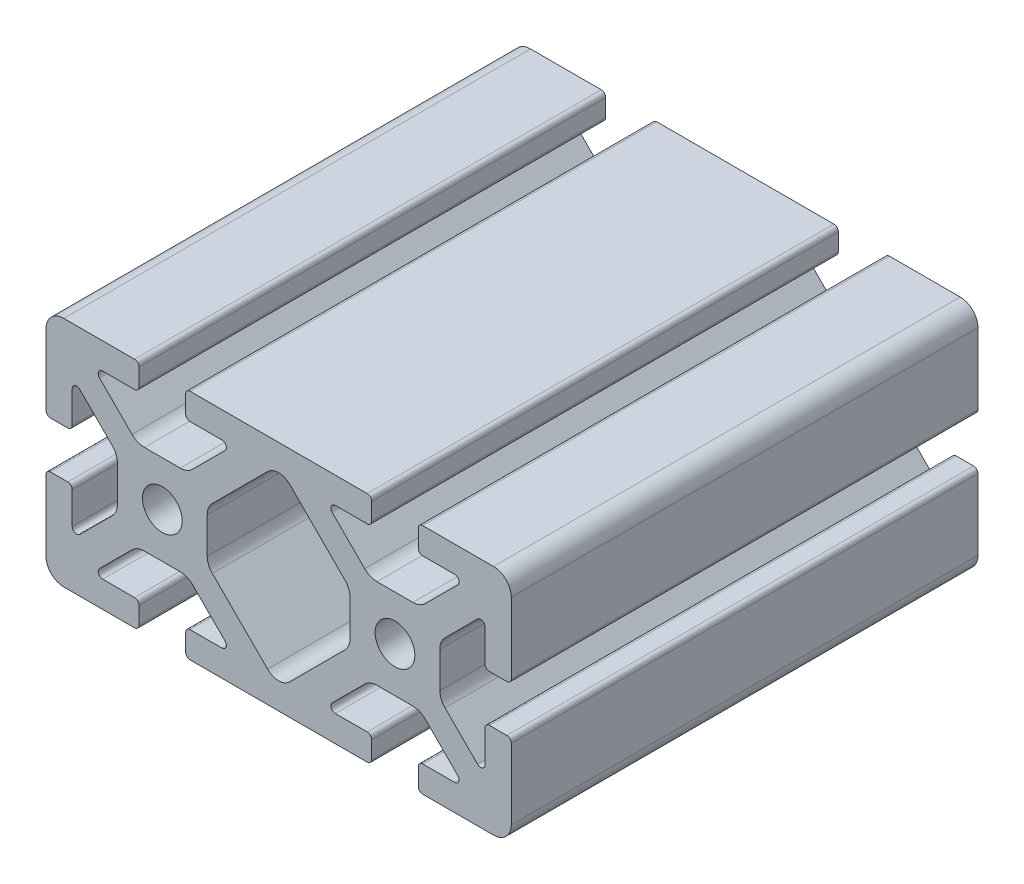
SolidWorks part; units mm, degrees
ref_plane "Front Plane" through (0, 0, 0) normal (0, 0, 1) x (1, 0, 0)
ref_plane "Top Plane" through (0, 0, 0) normal (0, 1, 0) x (1, 0, 0)
ref_plane "Right Plane" through (0, 0, 0) normal (1, 0, 0) x (0, 0, -1)
sketch "Sketch1" plane through (0, 0, 0) normal (0, 0, 1) x (1, 0, 0)
  line L2 (-39.878, 16.891) -> (-39.878, 4.7625)
  line L3 (-36.83, 19.939) -> (-24.7015, 19.939)
  line L4 (-23.9395, 19.177) -> (-23.9395, 16.2052)
  line L5 (-24.7015, 15.4432) -> (-30.1625, 15.4432)
  line L6 (-30.7013, 14.1424) -> (-25.133, 8.5741)
  line L7 (-34.0814, 10.7623) -> (-28.5131, 5.194)
  line L8 (-35.3822, 10.2235) -> (-35.3822, 4.7625)
  line L9 (-36.1442, 4.0005) -> (-39.116, 4.0005)
  line L11 (-23.0136, 7.6962) -> (-16.8644, 7.6962)
  line L12 (-27.6352, 3.0746) -> (-27.6352, -3.0746)
  line L13 (15.1765, 19.939) -> (-15.1765, 19.939)
  line L14 (-15.9385, 19.177) -> (-15.9385, 16.2052)
  line L15 (-15.1765, 15.4432) -> (-9.7155, 15.4432)
  line L16 (-12.2428, 3.0746) -> (-12.2428, -3.0746)
  line L17 (-9.1767, 14.1424) -> (-14.745, 8.5741)
  line L18 (-1.9047, 14.6543) -> (-11.3649, 5.194)
  line L19 (-36.1442, -4.0005) -> (-39.116, -4.0005)
  line L20 (-35.3822, -10.2235) -> (-35.3822, -4.7625)
  line L21 (-34.0814, -10.7623) -> (-28.5131, -5.194)
  line L22 (-30.7013, -14.1424) -> (-25.133, -8.5741)
  line L23 (-24.7015, -15.4432) -> (-30.1625, -15.4432)
  line L24 (-23.9395, -19.177) -> (-23.9395, -16.2052)
  line L25 (-36.83, -19.939) -> (-24.7015, -19.939)
  line L26 (-39.878, -16.891) -> (-39.878, -4.7625)
  line L27 (15.1765, -19.939) -> (-15.1765, -19.939)
  line L28 (-15.9385, -19.177) -> (-15.9385, -16.2052)
  line L29 (-15.1765, -15.4432) -> (-9.7155, -15.4432)
  line L30 (-9.1767, -14.1424) -> (-14.745, -8.5741)
  line L31 (-1.9047, -14.6543) -> (-11.3649, -5.194)
  line L32 (-23.0136, -7.6962) -> (-16.8644, -7.6962)
  line L34 (23.0136, -7.6962) -> (16.8644, -7.6962)
  line L35 (1.9047, -14.6543) -> (11.3649, -5.194)
  line L36 (9.1767, -14.1424) -> (14.745, -8.5741)
  line L37 (15.1765, -15.4432) -> (9.7155, -15.4432)
  line L38 (15.9385, -19.177) -> (15.9385, -16.2052)
  line L40 (39.878, -16.891) -> (39.878, -4.7625)
  line L41 (36.83, -19.939) -> (24.7015, -19.939)
  line L42 (23.9395, -19.177) -> (23.9395, -16.2052)
  line L43 (24.7015, -15.4432) -> (30.1625, -15.4432)
  line L44 (30.7013, -14.1424) -> (25.133, -8.5741)
  line L45 (34.0814, -10.7623) -> (28.5131, -5.194)
  line L46 (35.3822, -10.2235) -> (35.3822, -4.7625)
  line L47 (36.1442, -4.0005) -> (39.116, -4.0005)
  line L48 (1.9047, 14.6543) -> (11.3649, 5.194)
  line L49 (9.1767, 14.1424) -> (14.745, 8.5741)
  line L50 (12.2428, 3.0746) -> (12.2428, -3.0746)
  line L51 (15.1765, 15.4432) -> (9.7155, 15.4432)
  line L52 (15.9385, 19.177) -> (15.9385, 16.2052)
  line L53 (27.6352, 3.0746) -> (27.6352, -3.0746)
  line L54 (23.0136, 7.6962) -> (16.8644, 7.6962)
  line L55 (36.1442, 4.0005) -> (39.116, 4.0005)
  line L56 (35.3822, 10.2235) -> (35.3822, 4.7625)
  line L57 (34.0814, 10.7623) -> (28.5131, 5.194)
  line L58 (30.7013, 14.1424) -> (25.133, 8.5741)
  line L59 (24.7015, 15.4432) -> (30.1625, 15.4432)
  line L60 (23.9395, 19.177) -> (23.9395, 16.2052)
  line L61 (36.83, 19.939) -> (24.7015, 19.939)
  line L62 (39.878, 16.891) -> (39.878, 4.7625)
  circle A0 centre (-19.939, 0) radius 3.4036
  arc A1 (-39.878, 16.891) -> (-36.83, 19.939) centre (-36.83, 16.891) cw
  arc A2 (-34.0814, 10.7623) -> (-35.3822, 10.2235) centre (-34.6202, 10.2235) ccw
  arc A3 (-30.1625, 15.4432) -> (-30.7013, 14.1424) centre (-30.1625, 14.6812) ccw
  arc A4 (-24.7015, 19.939) -> (-23.9395, 19.177) centre (-24.7015, 19.177) cw
  arc A5 (-39.878, 4.7625) -> (-39.116, 4.0005) centre (-39.116, 4.7625) ccw
  arc A6 (-35.3822, 4.7625) -> (-36.1442, 4.0005) centre (-36.1442, 4.7625) cw
  arc A7 (-23.9395, 16.2052) -> (-24.7015, 15.4432) centre (-24.7015, 16.2052) cw
  arc A8 (-23.0136, 7.6962) -> (-25.133, 8.5741) centre (-23.0136, 10.6934) cw
  arc A9 (-27.6352, 3.0746) -> (-28.5131, 5.194) centre (-30.6324, 3.0746) ccw
  arc A10 (1.9047, 14.6543) -> (-1.9047, 14.6543) centre (0, 12.7496) ccw
  arc A11 (-1.9047, -14.6543) -> (1.9047, -14.6543) centre (0, -12.7496) ccw
  arc A12 (-15.1765, 19.939) -> (-15.9385, 19.177) centre (-15.1765, 19.177) ccw
  arc A13 (-15.9385, 16.2052) -> (-15.1765, 15.4432) centre (-15.1765, 16.2052) ccw
  arc A14 (-16.8644, 7.6962) -> (-14.745, 8.5741) centre (-16.8644, 10.6934) ccw
  arc A15 (-12.2428, 3.0746) -> (-11.3649, 5.194) centre (-9.2456, 3.0746) cw
  arc A16 (-9.7155, 15.4432) -> (-9.1767, 14.1424) centre (-9.7155, 14.6812) cw
  arc A17 (-27.6352, -3.0746) -> (-28.5131, -5.194) centre (-30.6324, -3.0746) cw
  arc A18 (-23.0136, -7.6962) -> (-25.133, -8.5741) centre (-23.0136, -10.6934) ccw
  arc A19 (-23.9395, -16.2052) -> (-24.7015, -15.4432) centre (-24.7015, -16.2052) ccw
  arc A20 (-35.3822, -4.7625) -> (-36.1442, -4.0005) centre (-36.1442, -4.7625) ccw
  arc A21 (-39.878, -4.7625) -> (-39.116, -4.0005) centre (-39.116, -4.7625) cw
  arc A22 (-24.7015, -19.939) -> (-23.9395, -19.177) centre (-24.7015, -19.177) ccw
  arc A23 (-30.1625, -15.4432) -> (-30.7013, -14.1424) centre (-30.1625, -14.6812) cw
  arc A24 (-34.0814, -10.7623) -> (-35.3822, -10.2235) centre (-34.6202, -10.2235) cw
  arc A25 (-39.878, -16.891) -> (-36.83, -19.939) centre (-36.83, -16.891) ccw
  arc A26 (-9.7155, -15.4432) -> (-9.1767, -14.1424) centre (-9.7155, -14.6812) ccw
  arc A27 (-15.1765, -19.939) -> (-15.9385, -19.177) centre (-15.1765, -19.177) cw
  arc A28 (-15.9385, -16.2052) -> (-15.1765, -15.4432) centre (-15.1765, -16.2052) cw
  arc A29 (-16.8644, -7.6962) -> (-14.745, -8.5741) centre (-16.8644, -10.6934) cw
  arc A30 (-12.2428, -3.0746) -> (-11.3649, -5.194) centre (-9.2456, -3.0746) ccw
  arc A31 (12.2428, -3.0746) -> (11.3649, -5.194) centre (9.2456, -3.0746) cw
  arc A32 (16.8644, -7.6962) -> (14.745, -8.5741) centre (16.8644, -10.6934) ccw
  arc A33 (15.9385, -16.2052) -> (15.1765, -15.4432) centre (15.1765, -16.2052) ccw
  arc A34 (15.1765, -19.939) -> (15.9385, -19.177) centre (15.1765, -19.177) ccw
  arc A35 (9.7155, -15.4432) -> (9.1767, -14.1424) centre (9.7155, -14.6812) cw
  arc A36 (39.878, -16.891) -> (36.83, -19.939) centre (36.83, -16.891) cw
  arc A37 (34.0814, -10.7623) -> (35.3822, -10.2235) centre (34.6202, -10.2235) ccw
  arc A38 (30.1625, -15.4432) -> (30.7013, -14.1424) centre (30.1625, -14.6812) ccw
  arc A39 (24.7015, -19.939) -> (23.9395, -19.177) centre (24.7015, -19.177) cw
  arc A40 (39.878, -4.7625) -> (39.116, -4.0005) centre (39.116, -4.7625) ccw
  arc A41 (35.3822, -4.7625) -> (36.1442, -4.0005) centre (36.1442, -4.7625) cw
  arc A42 (23.9395, -16.2052) -> (24.7015, -15.4432) centre (24.7015, -16.2052) cw
  arc A43 (23.0136, -7.6962) -> (25.133, -8.5741) centre (23.0136, -10.6934) cw
  arc A44 (27.6352, -3.0746) -> (28.5131, -5.194) centre (30.6324, -3.0746) ccw
  arc A45 (9.7155, 15.4432) -> (9.1767, 14.1424) centre (9.7155, 14.6812) ccw
  arc A46 (12.2428, 3.0746) -> (11.3649, 5.194) centre (9.2456, 3.0746) ccw
  arc A47 (16.8644, 7.6962) -> (14.745, 8.5741) centre (16.8644, 10.6934) cw
  arc A48 (15.9385, 16.2052) -> (15.1765, 15.4432) centre (15.1765, 16.2052) cw
  arc A49 (15.1765, 19.939) -> (15.9385, 19.177) centre (15.1765, 19.177) cw
  arc A50 (27.6352, 3.0746) -> (28.5131, 5.194) centre (30.6324, 3.0746) cw
  arc A51 (23.0136, 7.6962) -> (25.133, 8.5741) centre (23.0136, 10.6934) ccw
  arc A52 (23.9395, 16.2052) -> (24.7015, 15.4432) centre (24.7015, 16.2052) ccw
  arc A53 (35.3822, 4.7625) -> (36.1442, 4.0005) centre (36.1442, 4.7625) ccw
  arc A54 (39.878, 4.7625) -> (39.116, 4.0005) centre (39.116, 4.7625) cw
  arc A55 (24.7015, 19.939) -> (23.9395, 19.177) centre (24.7015, 19.177) ccw
  arc A56 (30.1625, 15.4432) -> (30.7013, 14.1424) centre (30.1625, 14.6812) cw
  arc A57 (34.0814, 10.7623) -> (35.3822, 10.2235) centre (34.6202, 10.2235) cw
  arc A58 (39.878, 16.891) -> (36.83, 19.939) centre (36.83, 16.891) ccw
  circle A59 centre (19.939, 0) radius 3.4036
  point P185 (19.939, 7.6962)
extrude "Boss-Extrude1" add sketch "Sketch1" along normal mid plane 304.8
sketch "Sketch2" plane through (0, 0, 0) normal (1, 0, 0) x (0, 0, -1)
  line L0 (-152.4, -19.939) -> (152.4, -19.939) construction
  line L1 (152.4, 19.939) -> (-72.4, 19.939)
  line L2 (152.4, 19.939) -> (152.4, -19.939)
  line L3 (152.4, -19.939) -> (-72.4, -19.939)
  line L4 (-72.4, 19.939) -> (-72.4, -19.939)
extrude "Cut-Extrude1" cut sketch "Sketch2" against normal blind 40 and the other way blind 40
